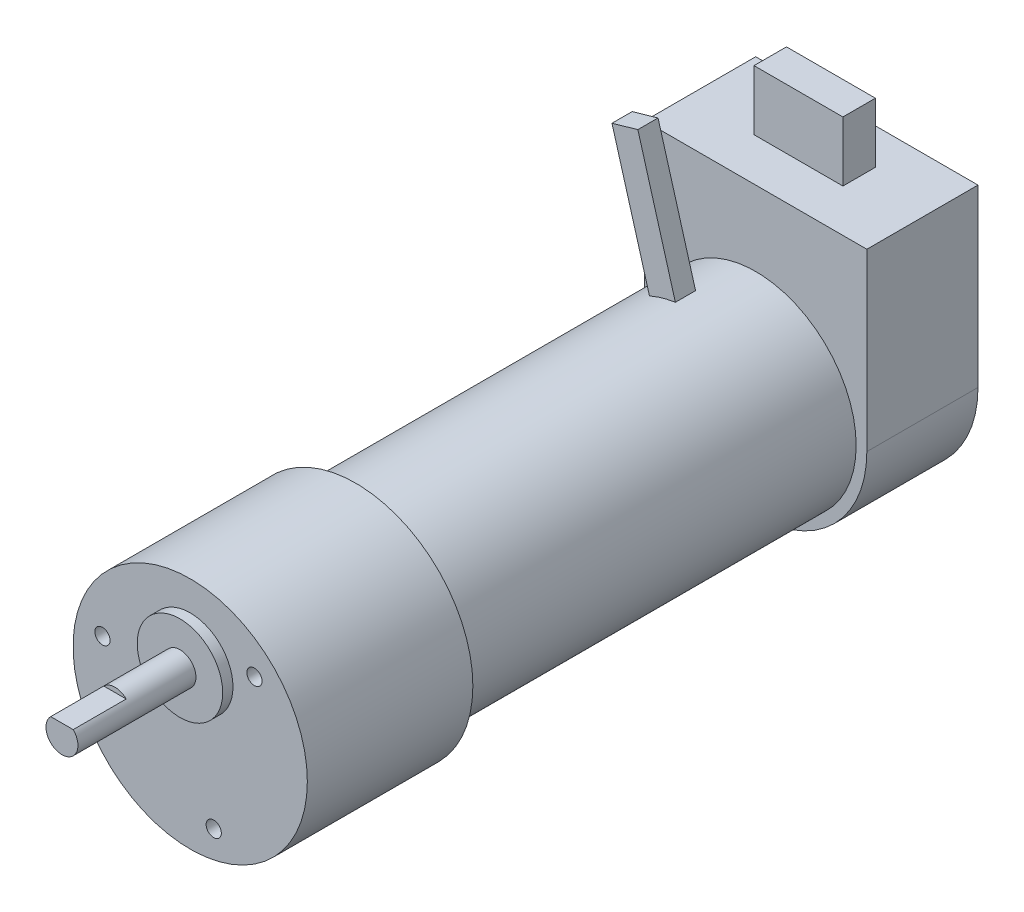
SolidWorks part; units mm, degrees
ref_plane "Front Plane" through (0, 0, 0) normal (0, 0, 1) x (1, 0, 0)
ref_plane "Top Plane" through (0, 0, 0) normal (0, 1, 0) x (1, 0, 0)
ref_plane "Right Plane" through (0, 0, 0) normal (1, 0, 0) x (0, 0, -1)
ref_axis "Axis1" through (0, 0, 55) along (0, 0, -1)
sketch "Sketch1" plane through (0, 0, 0) normal (1, 0, 0) x (0, 0, -1)
  line L0 (0, 0) -> (0, 17.399)
  line L1 (0, 17.399) -> (24.5872, 17.399)
  line L2 (24.5872, 17.399) -> (24.5872, 14.9225)
  line L3 (24.5872, 14.9225) -> (83.9978, 14.9225)
  line L4 (83.9978, 14.9225) -> (83.9978, 0)
  line L5 (-55, 0) -> (55, 0) construction
  line L6 (83.9978, 0) -> (0, 0)
  dimension "D1" = 14.9225
  dimension "D2" = 17.399
  dimension "D3" = 24.5872
  dimension "D4" = 83.9978
revolve "Revolve1" add sketch "Sketch1" angle 360 about axis through (0, 0, 55) along (0, 0, -1)
sketch "Sketch3" plane through (0, 0, -83.9978) normal (0, 0, -1) x (-1, 0, 0)
  line L0 (-16.51, 0) -> (-16.51, 26.035)
  line L1 (-16.51, 26.035) -> (16.51, 26.035)
  line L2 (16.51, 26.035) -> (16.51, 0)
  arc A0 (-16.51, 0) -> (16.51, 0) centre (0, 0) ccw
  dimension "D1" = 33.02
  dimension "D2" = 26.035
extrude "Boss-Extrude1" add sketch "Sketch3" along normal blind 16.51
sketch "Sketch4" plane through (0, 0, 0) normal (1, 0, 0) x (0, 0, -1)
  line L0 (100.5078, 26.035) -> (83.9978, 26.035) construction
  line L1 (90.3478, 26.035) -> (95.1738, 26.035)
  line L2 (90.3478, 26.035) -> (90.3478, 34.925)
  line L3 (90.3478, 34.925) -> (95.1738, 34.925)
  line L4 (95.1738, 26.035) -> (95.1738, 34.925)
  line L5 (83.9978, 26.035) -> (83.9978, 0) construction
  dimension "D1" = 8.89
  dimension "D2" = 4.826
  dimension "D3" = 6.35
extrude "Boss-Extrude2" add sketch "Sketch4" along normal mid plane 13.208
ref_plane "Plane1" through (0, 6.6548, 0) normal (0, 1, 0) x (-1, 0, 0)
ref_axis "Axis2" through (0, 6.6548, 5.0254) along (0, 0, -1)
sketch "Sketch5" plane through (0, 0, 0) normal (1, 0, 0) x (0, 0, -1)
  line L0 (0, 13.0048) -> (-1.524, 13.0048)
  line L1 (0, 17.399) -> (0, -17.399) construction
  line L2 (-1.524, 13.0048) -> (-1.524, 9.0297)
  line L3 (-1.524, 9.0297) -> (-19.05, 9.0297)
  line L4 (-19.05, 9.0297) -> (-19.05, 6.6548)
  line L5 (-5.0254, 6.6548) -> (105.5332, 6.6548) construction
  line L6 (-19.05, 6.6548) -> (0, 6.6548)
  line L7 (19.1389, 6.6548) -> (-19.1389, 6.6548) construction
  line L8 (0, 6.6548) -> (0, 13.0048)
  dimension "D1" = 1.524
  dimension "D2" = 19.05
  dimension "D3" = 6.35
  dimension "D4" = 2.3749
revolve "Revolve2" add sketch "Sketch5" angle 360 about axis through (0, 6.6548, 5.0254) along (0, 0, -1)
sketch "Sketch6" plane through (0, 0, 19.05) normal (0, 0, 1) x (1, 0, 0)
  line L0 (-1.6695, 8.3439) -> (1.6695, 8.3439)
  line L1 (0, 8.3439) -> (0, 4.2799) construction
  circle A0 centre (0, 6.6548) radius 2.3749 construction
  circle A1 centre (0, 6.6548) radius 2.3749
  arc A2 (1.6695, 8.3439) -> (-1.6695, 8.3439) centre (0, 6.6548) ccw
  circle A3 centre (0, 6.6548) radius 2.3749 construction
  dimension "D2" = 4.064
  dimension "D1" = 0
extrude "Cut-Extrude1" cut sketch "Sketch6" against normal blind 7.874
hole_wizard "#4-40 Tapped Hole1" positions "Sketch8" profile "Sketch7" tap size "#4-40" standard "Ansi Inch"
sketch "Sketch8" plane through (0, 0, 0) normal (0, 0, 1) x (1, 0, 0)
  line L0 (0, -14.2183) -> (0, 0) construction
  line L1 (0, 0) -> (3.4924, -13.034) construction
  point P0 (3.4924, -13.034)
  dimension "D1" = 15
  dimension "D2" = 13.4937
sketch "Sketch7" plane through (3.4924, -13.034, 0) normal (1, 0, 0) x (0, -1, 0)
  line L0 (0, 0) -> (0, 7.4092)
  line L1 (0, 7.4092) -> (1.1303, 6.73)
  line L2 (1.1303, 6.73) -> (1.1303, 0)
  line L5 (1.1303, 0) -> (0, 0)
  line L10 (0, 7.4092) -> (-1.1303, 6.73) construction
  line L11 (0, -6.35) -> (0, 107.95) construction
  dimension "Tap Drill Dia." = 2.2606
  dimension "Tap Drill Depth" = 6.73
  dimension "Drill Angle" = 118
cosmetic thread "Hole Thread1" parameters "D1"=4.826, "D2"=2.8448
pattern_circular "CirPattern1" count 3 over 360 about axis through (0, 0, 0) along (0, 0, 1) of "#4-40 Tapped Hole1"
sketch "Sketch9" plane through (0, 0, -100.5078) normal (0, 0, -1) x (-1, 0, 0)
  line L0 (0, 0) -> (14.87, 51.8579) construction
  line L1 (0, 0) -> (0, 50.1437) construction
  line L2 (0, 0) -> (-1.9225, 0.5513)
  line L3 (-1.9225, 0.5513) -> (7.7248, 34.1954)
  line L4 (7.7248, 34.1954) -> (11.5698, 33.0929)
  line L5 (11.5698, 33.0929) -> (1.9225, -0.5513)
  line L6 (1.9225, -0.5513) -> (0, 0)
  dimension "D1" = 16
  dimension "D2" = 4
  dimension "D3" = 35
extrude "Boss-Extrude3" add sketch "Sketch9" against normal blind 3 from offset 23.29 offset against normal yes
